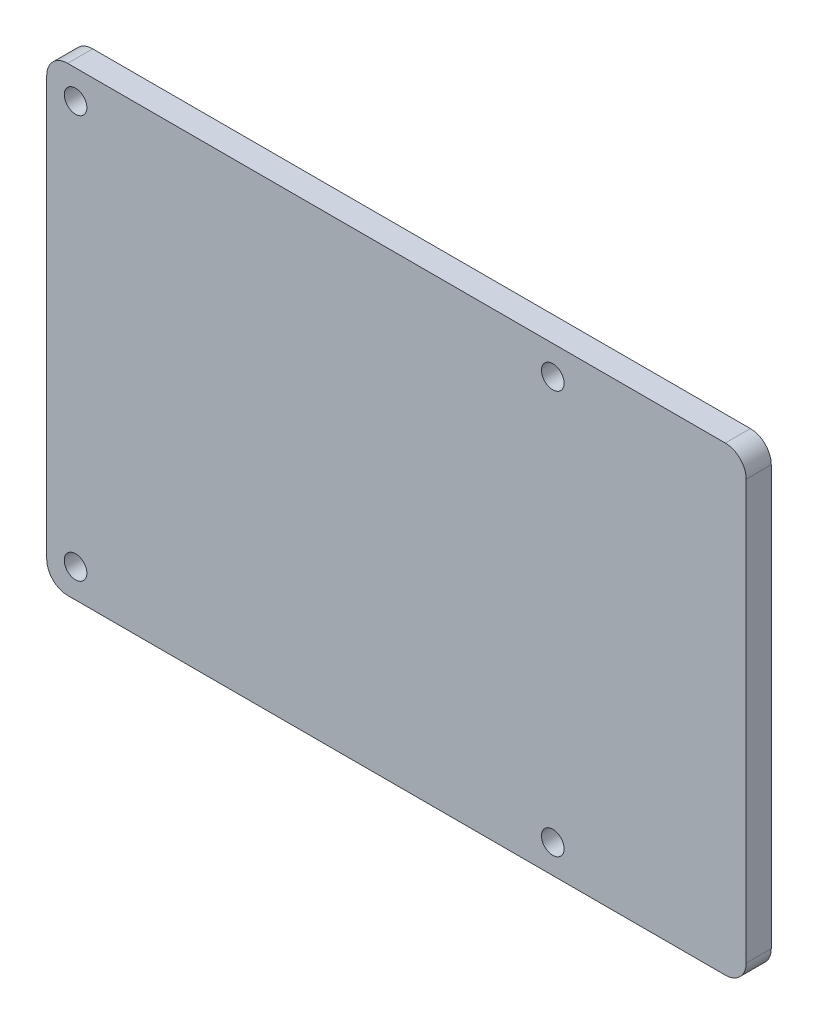
SolidWorks part; units mm, degrees
ref_plane "Front Plane" through (0, 0, 0) normal (0, 0, 1) x (1, 0, 0)
ref_plane "Top Plane" through (0, 0, 0) normal (0, 1, 0) x (1, 0, 0)
ref_plane "Right Plane" through (0, 0, 0) normal (1, 0, 0) x (0, 0, -1)
sketch "Sketch1" plane through (0, 0, 0) normal (0, 0, 1) x (1, 0, 0)
  line L0 (-2.1296, -12.975) -> (82.8796, -12.975) construction
  line L1 (-2.125, 12.025) -> (-2.1343, -37.975) construction
  line L2 (0.875, -40.975) -> (79.875, -40.9843) construction
  line L3 (82.875, -37.975) -> (82.8843, 12.025) construction
  line L4 (0.4104, 15.0296) -> (80.3396, 15.0296)
  line L5 (-2.1296, 12.4896) -> (-2.1296, -38.4396)
  line L6 (0.4104, -40.9796) -> (80.3396, -40.9796)
  line L7 (82.8796, 12.4896) -> (82.8796, -38.4396)
  line L9 (40.375, 15.0296) -> (40.375, -40.9796) construction
  line L11 (79.875, 15.025) -> (0.875, 15.0343) construction
  circle A0 centre (1.375, 11.525) radius 1.375
  circle A1 centre (59.375, 11.525) radius 1.375
  circle A2 centre (59.375, -37.475) radius 1.375
  circle A3 centre (1.375, -37.475) radius 1.375
  arc A4 (80.3396, 15.0296) -> (82.8796, 12.4896) centre (80.3396, 12.4896) cw
  arc A5 (82.8796, -38.4396) -> (80.3396, -40.9796) centre (80.3396, -38.4396) cw
  arc A6 (0.4104, -40.9796) -> (-2.1296, -38.4396) centre (0.4104, -38.4396) cw
  arc A7 (-2.1296, 12.4896) -> (0.4104, 15.0296) centre (0.4104, 12.4896) cw
  dimension "D1" = 2.54
  dimension "D2" = 2.75
  dimension "D3" = 2.75
  dimension "D4" = 2.75
  dimension "D5" = 2.75
extrude "Boss-Extrude1" add sketch "Sketch1" against normal blind 3.048 contours L5 A6 L6 A5 L7 A4 L4 A7
